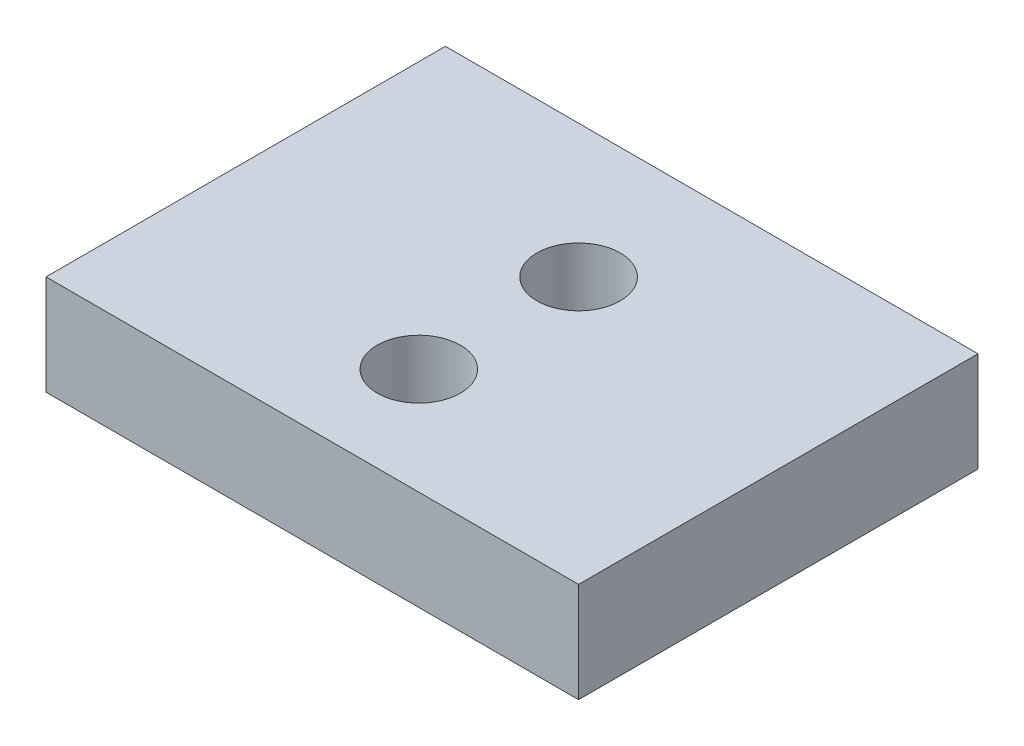
SolidWorks part; units mm, degrees
ref_plane "Front Plane" through (0, 0, 0) normal (0, 0, 1) x (1, 0, 0)
ref_plane "Top Plane" through (0, 0, 0) normal (0, 1, 0) x (1, 0, 0)
ref_plane "Right Plane" through (0, 0, 0) normal (1, 0, 0) x (0, 0, -1)
sketch "Sketch1" plane through (0, 0, 0) normal (0, 0, 1) x (1, 0, 0)
  line L0 (-25.4, -50.8) -> (-25.4, 50.8) construction
  line L1 (25.4, -4.7625) -> (-25.4, -4.7625)
  line L2 (25.4, -4.7625) -> (25.4, 4.7625)
  line L3 (25.4, 4.7625) -> (-25.4, 4.7625)
  line L4 (-25.4, -4.7625) -> (-25.4, 4.7625)
  line L5 (25.4, -4.7625) -> (-25.4, 4.7625) construction
  line L6 (25.4, 4.7625) -> (-25.4, -4.7625) construction
  circle A1 centre (-12.7, 0) radius 2.2479 construction
  circle A2 centre (12.7, 0) radius 2.2479 construction
  circle A5 centre (-12.7, 0) radius 2.2479
  circle A6 centre (12.7, 0) radius 2.2479
  point P0 (0, 0)
  dimension "D1" = 9.525
extrude "Boss-Extrude1" add sketch "Sketch1" along normal blind 38.1 contours L1 L4 L3 L2
hole_wizard "5/16 (0.3125) Diameter Hole1" positions "Sketch4" profile "Sketch5" hole size "5/16" standard "ANSI Inch" end condition through all
sketch "Sketch4" plane through (0, -4.7625, 0) normal (0, -1, 0) x (-1, 0, 0)
  line L0 (-25.4, -38.1) -> (25.4, -38.1) construction
  point P0 (0, -12.7)
  point P2 (0, -27.94)
  point P7 (0, -38.1)
  dimension "D1" = 15.24
  dimension "D2" = 10.16
sketch "Sketch5" plane through (0, -4.7625, 12.7) normal (1, 0, 0) x (0, 0, -1)
  line L0 (0, 0) -> (0, 9.525)
  line L1 (0, 9.525) -> (3.9687, 9.525)
  line L2 (3.9687, 9.525) -> (3.9688, 0)
  line L5 (3.9688, 0) -> (0, 0)
  line L11 (0, -6.35) -> (0, 107.95) construction
  dimension "Thru Hole Dia." = 7.9375
  dimension "Thru Hole Depth" = 9.525
hole_wizard "#8-32 Tapped Hole1" positions "Sketch8" profile "Sketch7" tap size "#8-32" standard "ANSI Inch"
sketch "Sketch8" plane through (0, 0, 0) normal (0, 0, -1) x (-1, 0, 0)
  point P2 (-12.7, 0)
  point P4 (12.7, 0)
  point P18 (0, 0)
  point P19 (0, 0)
cosmetic thread "Hole Thread2" parameters "D2"=4.1656
cosmetic thread "Hole Thread3" parameters "D2"=4.1656
sketch "Sketch7" plane through (12.7, 0, 0) normal (1, 0, 0) x (0, 1, 0)
  line L0 (0, 0) -> (0, 26.4378)
  line L1 (0, 26.4378) -> (1.7272, 25.4)
  line L2 (1.7272, 25.4) -> (1.7272, 0)
  line L5 (1.7272, 0) -> (0, 0)
  line L10 (0, 26.4378) -> (-1.7272, 25.4) construction
  line L11 (0, -6.35) -> (0, 107.95) construction
  dimension "Tap Drill Dia." = 3.4544
  dimension "Tap Drill Depth" = 25.4
  dimension "Drill Angle" = 118
equation "\"TabDepth\"= 1.5"
equation "\"D1@Boss-Extrude1\"=\"TabDepth\""
